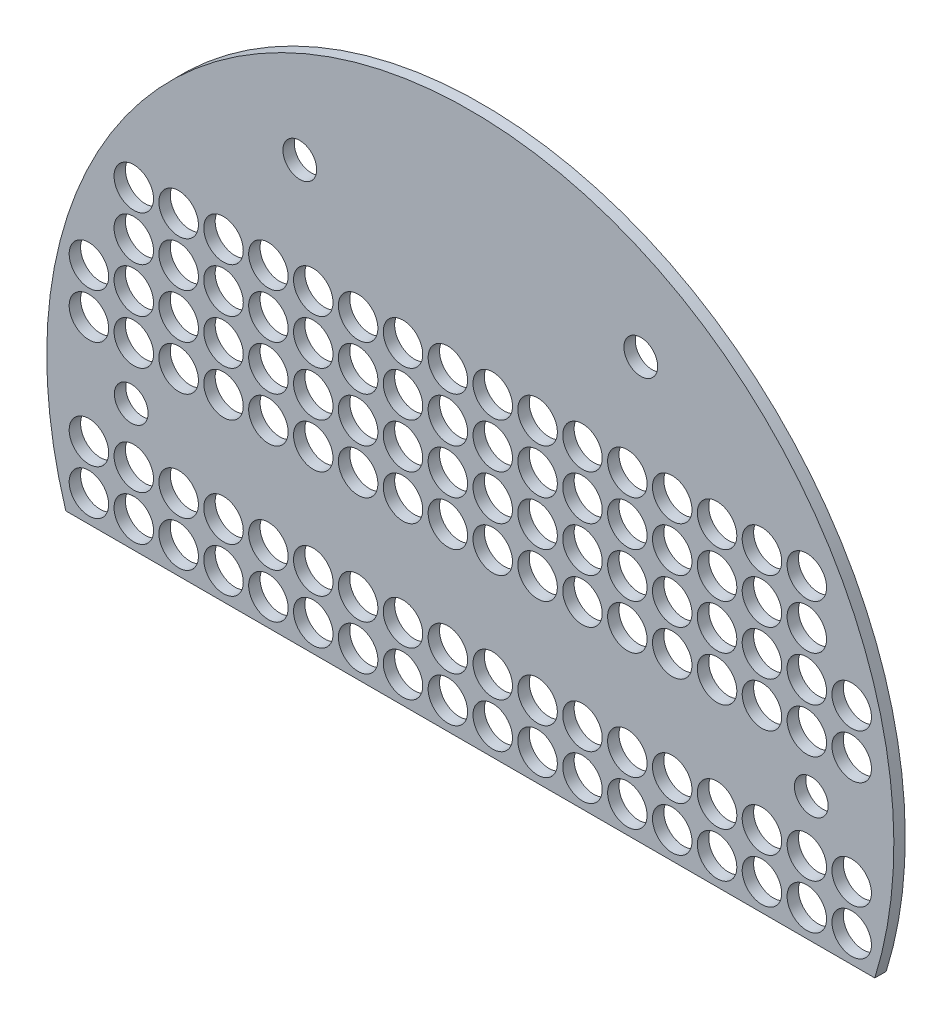
SolidWorks part; units mm, degrees
ref_plane "Front Plane" through (0, 0, 0) normal (0, 0, 1) x (1, 0, 0)
ref_plane "Top Plane" through (0, 0, 0) normal (0, 1, 0) x (1, 0, 0)
ref_plane "Right Plane" through (0, 0, 0) normal (1, 0, 0) x (0, 0, -1)
sketch "Sketch1" plane through (0, 0, 0) normal (0, 0, 1) x (1, 0, 0)
  line L0 (-236.5407, -0.9462) -> (235.4593, -0.9462) construction
  line L1 (-225.9205, -70.946) -> (224.8391, -70.946)
  arc A0 (234.5553, 19.6906) -> (-235.6367, 19.6906) centre (-0.5407, -0.9462) ccw
  circle A1 centre (-213.0407, -55.9462) radius 11
  circle A2 centre (-188.0407, -55.9462) radius 11
  circle A3 centre (-138.0407, -55.9462) radius 11
  circle A4 centre (-113.0407, -55.9462) radius 11
  circle A5 centre (-88.0407, -55.9462) radius 11
  circle A6 centre (-63.0407, -55.9462) radius 11
  circle A7 centre (-38.0407, -55.9462) radius 11
  circle A8 centre (-13.0407, -55.9462) radius 11
  circle A9 centre (211.9593, -55.9462) radius 11
  circle A10 centre (211.9593, -30.9462) radius 11
  circle A11 centre (186.9593, -55.9462) radius 11
  circle A12 centre (186.9593, -30.9462) radius 11
  circle A13 centre (161.9593, -30.9462) radius 11
  circle A14 centre (161.9593, -55.9462) radius 11
  circle A15 centre (136.9593, -55.9462) radius 11
  circle A16 centre (136.9593, -30.9462) radius 11
  circle A17 centre (111.9593, -30.9462) radius 11
  circle A18 centre (111.9593, -55.9462) radius 11
  circle A19 centre (86.9593, -55.9462) radius 11
  circle A20 centre (86.9593, -30.9462) radius 11
  circle A21 centre (61.9593, -55.9462) radius 11
  circle A22 centre (61.9593, -30.9462) radius 11
  circle A23 centre (36.9593, -55.9462) radius 11
  circle A24 centre (36.9593, -30.9462) radius 11
  circle A25 centre (11.9593, -30.9462) radius 11
  circle A26 centre (-13.0407, -30.9462) radius 11
  circle A27 centre (-38.0407, -30.9462) radius 11
  circle A28 centre (-63.0407, -30.9462) radius 11
  circle A29 centre (-88.0407, -30.9462) radius 11
  circle A30 centre (-113.0407, -30.9462) radius 11
  circle A31 centre (-138.0407, -30.9462) radius 11
  circle A32 centre (-163.0407, -30.9462) radius 11
  circle A33 centre (-188.0407, -30.9462) radius 11
  circle A34 centre (-213.0407, -30.9462) radius 11
  circle A35 centre (94.4593, 163.5986) radius 9.398
  circle A36 centre (-95.5407, 163.5986) radius 9.398
  circle A37 centre (-63.0407, 29.0538) radius 11
  circle A38 centre (-38.0407, 29.0538) radius 11
  circle A39 centre (-38.0407, 54.0538) radius 11
  circle A40 centre (-63.0407, 54.0538) radius 11
  circle A41 centre (-63.0407, 79.0538) radius 11
  circle A42 centre (-38.0407, 79.0538) radius 11
  circle A43 centre (-13.0407, 79.0538) radius 11
  circle A44 centre (-13.0407, 54.0538) radius 11
  circle A45 centre (-13.0407, 29.0538) radius 11
  circle A46 centre (11.9593, 29.0538) radius 11
  circle A47 centre (11.9593, 54.0538) radius 11
  circle A48 centre (11.9593, 79.0538) radius 11
  circle A49 centre (36.9593, 79.0538) radius 11
  circle A50 centre (36.9593, 54.0538) radius 11
  circle A51 centre (36.9593, 29.0538) radius 11
  circle A52 centre (61.9593, 29.0538) radius 11
  circle A53 centre (61.9593, 79.0538) radius 11
  circle A54 centre (61.9593, 54.0538) radius 11
  circle A55 centre (86.9593, 54.0538) radius 11
  circle A56 centre (86.9593, 29.0538) radius 11
  circle A57 centre (86.9593, 79.0538) radius 11
  circle A58 centre (111.9593, 79.0538) radius 11
  circle A59 centre (111.9593, 54.0538) radius 11
  circle A60 centre (111.9593, 29.0538) radius 11
  circle A61 centre (136.9593, 29.0538) radius 11
  circle A62 centre (136.9593, 54.0538) radius 11
  circle A63 centre (136.9593, 79.0538) radius 11
  circle A64 centre (161.9593, 79.0538) radius 11
  circle A65 centre (161.9593, 54.0538) radius 11
  circle A66 centre (161.9593, 29.0538) radius 11
  circle A67 centre (186.9593, 29.0538) radius 11
  circle A68 centre (211.9593, 29.0538) radius 11
  circle A69 centre (211.9593, 54.0538) radius 11
  circle A70 centre (186.9593, 54.0538) radius 11
  circle A71 centre (186.9593, 79.0538) radius 11
  circle A72 centre (186.9593, 104.0538) radius 11
  circle A73 centre (161.9593, 104.0538) radius 11
  circle A74 centre (136.9593, 104.0538) radius 11
  circle A75 centre (111.9593, 104.0538) radius 11
  circle A76 centre (86.9593, 104.0538) radius 11
  circle A77 centre (61.9593, 104.0538) radius 11
  circle A78 centre (36.9593, 104.0538) radius 11
  circle A79 centre (11.9593, 104.0538) radius 11
  circle A80 centre (-13.0407, 104.0538) radius 11
  circle A81 centre (-38.0407, 104.0538) radius 11
  circle A82 centre (-63.0407, 104.0538) radius 11
  circle A83 centre (-88.0407, 104.0538) radius 11
  circle A84 centre (-88.0407, 79.0538) radius 11
  circle A85 centre (-88.0407, 54.0538) radius 11
  circle A86 centre (-88.0407, 29.0538) radius 11
  circle A87 centre (-113.0407, 29.0538) radius 11
  circle A88 centre (-113.0407, 54.0538) radius 11
  circle A89 centre (-113.0407, 79.0538) radius 11
  circle A90 centre (-113.0407, 104.0538) radius 11
  circle A91 centre (-138.0407, 104.0538) radius 11
  circle A92 centre (-138.0407, 79.0538) radius 11
  circle A93 centre (-138.0407, 54.0538) radius 11
  circle A94 centre (-138.0407, 29.0538) radius 11
  circle A95 centre (-163.0407, 29.0538) radius 11
  circle A96 centre (-163.0407, 54.0538) radius 11
  circle A97 centre (-163.0407, 104.0538) radius 11
  circle A98 centre (-188.0407, 79.0538) radius 11
  circle A99 centre (-163.0407, 79.0538) radius 11
  circle A100 centre (-188.0407, 104.0538) radius 11
  circle A101 centre (-188.0407, 54.0538) radius 11
  circle A102 centre (-188.0407, 29.0538) radius 11
  circle A103 centre (-213.0407, 29.0538) radius 11
  circle A104 centre (-213.0407, 54.0538) radius 11
  arc A105 (-235.6367, -21.583) -> (-225.9205, -70.946) centre (-0.5407, -0.9462) ccw
  arc A106 (224.8391, -70.946) -> (-225.9205, -70.946) centre (-0.5407, -0.9462) ccw
  circle A108 centre (-163.0407, -55.9462) radius 11
  circle A109 centre (11.9593, -55.9462) radius 11
  arc A110 (224.8391, -70.946) -> (234.5553, -21.583) centre (-0.5407, -0.9462) ccw
  circle A111 centre (0, 0) radius 189.4532 construction
  circle A112 centre (-189.4509, -0.9462) radius 9.398
  circle A113 centre (189.4509, -0.9462) radius 9.398
extrude "Boss-Extrude1" add sketch "Sketch1" along normal mid plane 6.35 contours A106 L0 A0 A104 A103 A102 A101 A100 A99 A98 A97 A96 A95 A94 A93 A92 A91 A90 A89 A88 A87 A86 A85 A84 A83 A82 | L0 A106 A105 L1 A109 A108 A1 A2 A3 A4 A5 A6 A7 A8 A9 A10 A11 A12 A13 A14 A15 A16 A17 A18 A19 A20
